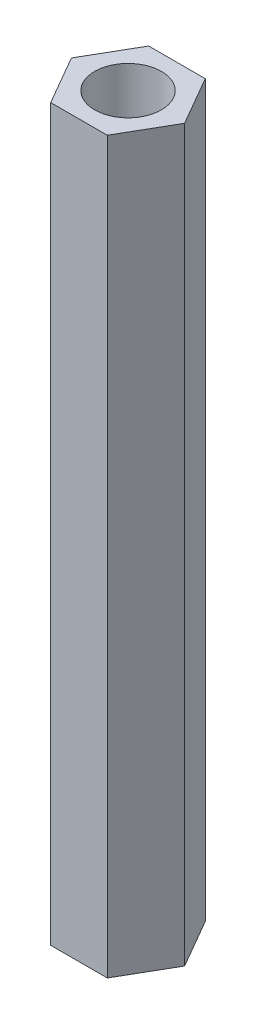
SolidWorks part; units mm, degrees
material "黄铜"
ref_plane "前视基准面" through (0, 0, 0) normal (0, 0, 1) x (1, 0, 0)
ref_plane "上视基准面" through (0, 0, 0) normal (0, 1, 0) x (1, 0, 0)
ref_plane "右视基准面" through (0, 0, 0) normal (1, 0, 0) x (0, 0, -1)
sketch "草图1" plane through (0, 0, 0) normal (0, 1, 0) x (1, 0, 0)
  line L1 (2.7135, 0) -> (1.3568, 2.35)
  line L2 (1.3568, 2.35) -> (-1.3568, 2.35)
  line L3 (-1.3568, 2.35) -> (-2.7135, 0)
  line L4 (-2.7135, 0) -> (-1.3568, -2.35)
  line L5 (-1.3568, -2.35) -> (1.3568, -2.35)
  line L6 (1.3568, -2.35) -> (2.7135, 0)
  circle A0 centre (0, 0) radius 2.35 construction
  dimension "D1" = 4.7
extrude "凸台-拉伸1" add sketch "草图1" along normal blind 35
sketch "草图2" plane through (0, 35, 0) normal (0, 1, 0) x (1, 0, 0)
  circle A0 centre (0, 0) radius 1.6
  dimension "D1" = 3.2
extrude "切除-拉伸1" cut sketch "草图2" against normal through all
